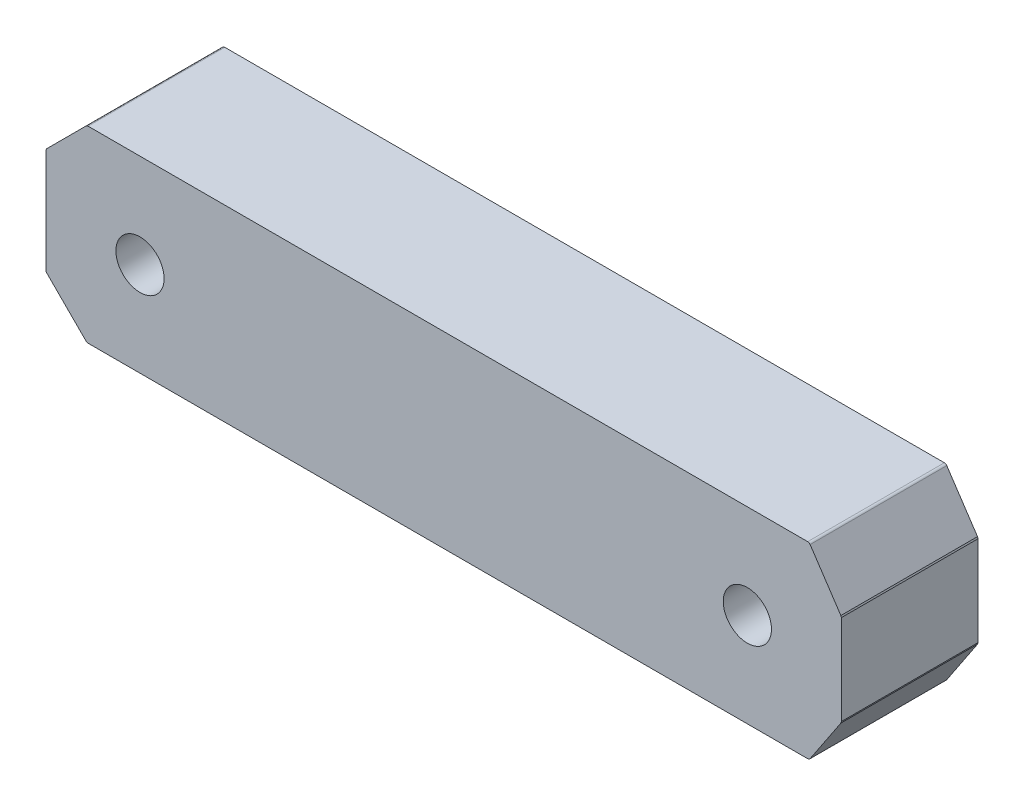
SolidWorks part; units mm, degrees
ref_plane "Front Plane" through (0, 0, 0) normal (0, 0, 1) x (1, 0, 0)
ref_plane "Top Plane" through (0, 0, 0) normal (0, 1, 0) x (1, 0, 0)
ref_plane "Right Plane" through (0, 0, 0) normal (1, 0, 0) x (0, 0, -1)
sketch "Sketch1" plane through (0, 0, 0) normal (0, 0, 1) x (1, 0, 0)
  line L0 (-24.7302, -6.4414) -> (-27.4414, -3.7302) construction
  line L1 (-24.7302, -6.4414) -> (-27.4414, -3.7302)
  line L2 (27.5, 3.111) -> (27.4664, 3.222)
  line L3 (-27.4414, 3.7302) -> (-24.7302, 6.4414) construction
  line L4 (27.4664, -3.222) -> (27.5, -3.111)
  line L6 (27.4664, -3.222) -> (25.3409, -6.4109) construction
  line L7 (27.5, 3.111) -> (27.5, -3.111) construction
  line L8 (25.3409, 6.4109) -> (27.4664, 3.222) construction
  line L10 (-27.5, -3.5887) -> (-27.5, 3.5887) construction
  line L11 (25.1745, 6.5) -> (-24.5887, 6.5)
  line L12 (-27.4414, 3.7302) -> (-24.7302, 6.4414)
  line L14 (-24.5887, -6.5) -> (25.1745, -6.5)
  line L15 (27.4664, -3.222) -> (25.3409, -6.4109)
  line L16 (27.5, 3.111) -> (27.5, -3.111)
  line L17 (25.3409, 6.4109) -> (27.4664, 3.222)
  line L19 (-27.5, -3.5887) -> (-27.5, 3.5887)
  arc A0 (-24.5887, 6.5) -> (-24.7302, 6.4414) centre (-24.5887, 6.3) ccw construction
  arc A1 (-27.4414, 3.7302) -> (-27.5, 3.5887) centre (-27.3, 3.5887) ccw construction
  arc A2 (-24.7302, -6.4414) -> (-24.5887, -6.5) centre (-24.5887, -6.3) ccw construction
  arc A3 (-27.5, -3.5887) -> (-27.4414, -3.7302) centre (-27.3, -3.5887) ccw construction
  arc A4 (25.1745, -6.5) -> (25.3409, -6.4109) centre (25.1745, -6.3) ccw construction
  arc A5 (25.3409, 6.4109) -> (25.1745, 6.5) centre (25.1745, 6.3) ccw construction
  circle A6 centre (21, 0) radius 1.666 construction
  circle A7 centre (-21, 0) radius 1.666 construction
  arc A8 (-24.5887, 6.5) -> (-24.7302, 6.4414) centre (-24.5887, 6.3) ccw
  arc A9 (-27.4414, 3.7302) -> (-27.5, 3.5887) centre (-27.3, 3.5887) ccw
  arc A10 (-24.7302, -6.4414) -> (-24.5887, -6.5) centre (-24.5887, -6.3) ccw
  arc A11 (-27.5, -3.5887) -> (-27.4414, -3.7302) centre (-27.3, -3.5887) ccw
  arc A12 (25.1745, -6.5) -> (25.3409, -6.4109) centre (25.1745, -6.3) ccw
  arc A13 (25.3409, 6.4109) -> (25.1745, 6.5) centre (25.1745, 6.3) ccw
  circle A14 centre (21, 0) radius 1.666
  circle A15 centre (-21, 0) radius 1.666
extrude "Boss-Extrude1" add sketch "Sketch1" along normal blind 9.45
